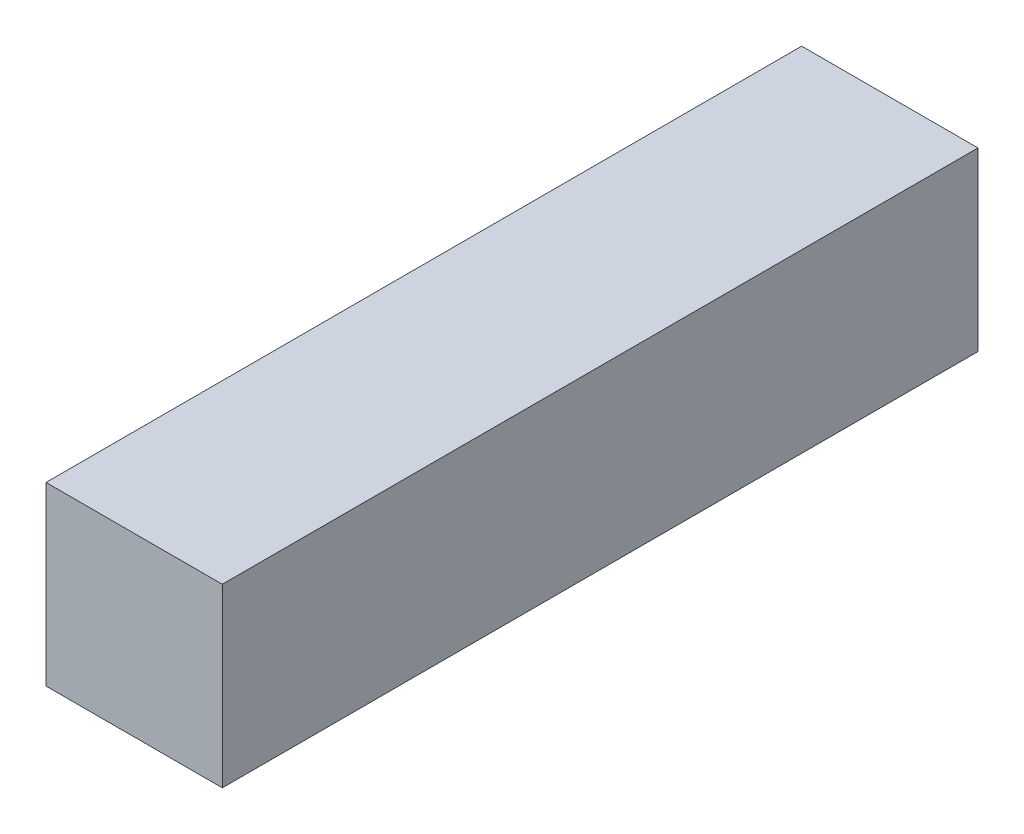
SolidWorks part; units mm, degrees
material "AISI 1020"
ref_plane "Спереди" through (0, 0, 0) normal (0, 0, 1) x (1, 0, 0)
ref_plane "Сверху" through (0, 0, 0) normal (0, 1, 0) x (1, 0, 0)
ref_plane "Справа" through (0, 0, 0) normal (1, 0, 0) x (0, 0, -1)
sketch "Эскиз1" plane through (0, 0, 0) normal (0, 0, 1) x (1, 0, 0)
  line L1 (-7, 7) -> (0, 7)
  line L2 (-7, 7) -> (-7, 0)
  line L3 (-7, 0) -> (0, 0)
  line L4 (0, 7) -> (0, 0)
extrude "Бобышка-Вытянуть1" add sketch "Эскиз1" against normal blind 30
